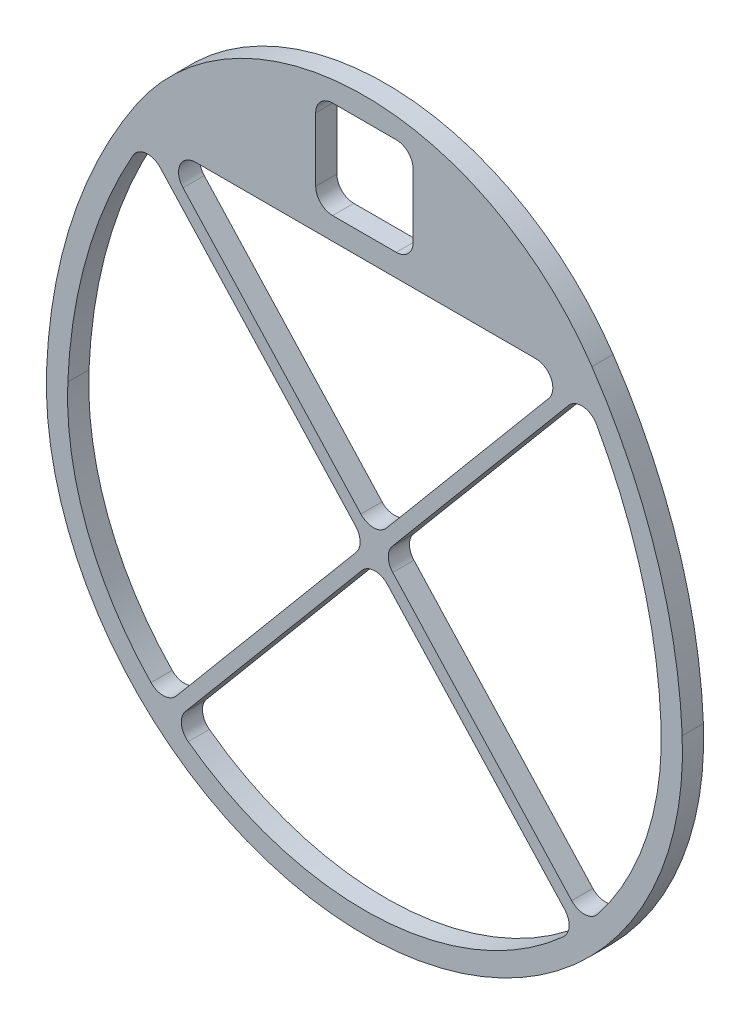
SolidWorks part; units mm, degrees
material "Balsa"
ref_plane "Front Plane" through (0, 0, 0) normal (0, 0, 1) x (1, 0, 0)
ref_plane "Top Plane" through (0, 0, 0) normal (0, 1, 0) x (1, 0, 0)
ref_plane "Right Plane" through (0, 0, 0) normal (1, 0, 0) x (0, 0, -1)
sketch "Sketch1" plane through (0, 0, 0) normal (0, 0, 1) x (1, 0, 0)
  line L8 (-88.9, 0) -> (88.9, 0) construction
  line L9 (-68.1884, 82.55) -> (68.1884, 82.55)
  line L10 (-64.77, 76.2) -> (64.77, 76.2)
  line L21 (-95.2446, 0.2624) -> (-88.9, 0)
  line L22 (88.9, 0) -> (95.2446, 0.2624)
  arc A0 (64.77, 76.2) -> (88.9, 0) centre (-63.3698, -6.2982) cw
  arc A1 (-64.77, 76.2) -> (-88.9, 0) centre (63.3698, -6.2982) ccw
  arc A2 (-68.1884, 82.55) -> (-95.2446, 0.2624) centre (63.3698, -6.2982) ccw
  arc A3 (68.1884, 82.55) -> (95.2446, 0.2624) centre (-63.3698, -6.2982) cw
  arc A4 (-70.1092, 79.6374) -> (-95.2446, 0.2624) centre (63.3698, -6.2982) ccw construction
  arc A5 (70.1092, 79.6374) -> (95.2446, 0.2624) centre (-63.3698, -6.2982) cw construction
  arc A6 (64.77, 76.2) -> (88.9, 0) centre (-63.3698, -6.2982) cw construction
  arc A7 (-64.77, 76.2) -> (-88.9, 0) centre (63.3698, -6.2982) ccw construction
  arc A8 (-68.1884, 82.55) -> (68.1884, 82.55) centre (0, 36.4988) cw
  arc A9 (-88.9, 0) -> (88.9, 0) centre (0, -3.6771) ccw
  arc A10 (-95.2446, 0.2624) -> (95.2446, 0.2624) centre (0, -3.6771) ccw
  point P0 (0, 0)
  point P13 (0, 76.2)
  dimension "D7" = 177.8
  dimension "D2" = 152.4
  dimension "D3" = 76.2
  dimension "D6" = 129.54
  dimension "D1" = 6.35
  dimension "D4" = 6.35
  dimension "D5" = 6.35
extrude "Boss-Extrude1" add sketch "Sketch1" along normal blind 6.35
sketch "Sketch2" plane through (0, 0, 6.35) normal (0, 0, 1) x (1, 0, 0)
  line L0 (0, 76.2) -> (0, 118.7811) construction
  line L1 (-14.605, 112.0955) -> (14.605, 112.0955)
  line L2 (-14.605, 112.0955) -> (-14.605, 82.8855)
  line L3 (-14.605, 82.8855) -> (14.605, 82.8855)
  line L4 (14.605, 112.0955) -> (14.605, 82.8855)
  line L5 (-14.605, 112.0955) -> (14.605, 82.8855) construction
  line L6 (-14.605, 82.8855) -> (14.605, 112.0955) construction
  line L7 (-64.77, 76.2) -> (64.77, 76.2) construction
  arc A0 (68.1884, 82.55) -> (-68.1884, 82.55) centre (0, 36.4988) ccw construction
  point P0 (0, 97.4905)
  point P15 (0, 97.4905)
  dimension "D1" = 29.21
  dimension "D2" = 29.21
extrude "Cut-Extrude1" cut sketch "Sketch2" against normal up to next
fillet "Fillet1" radius 5.08 4 edges at (14.605, 82.8855, 3.175) (14.605, 112.0955, 3.175) (-14.605, 112.0955, 3.175) (-14.605, 82.8855, 3.175)
sketch "Sketch3" plane through (0, 0, 6.35) normal (0, 0, 1) x (1, 0, 0)
  line L0 (-66.1729, 74.9112) -> (66.1428, -69.117)
  line L1 (-66.1729, 74.9112) -> (-63.3671, 77.4888)
  line L2 (66.1428, -69.117) -> (68.9485, -66.5394)
  line L3 (-63.3671, 77.4888) -> (68.9485, -66.5394)
  line L4 (63.3107, 77.4245) -> (-62.4057, -72.3985)
  line L5 (63.3107, 77.4245) -> (66.2293, 74.9755)
  line L6 (-62.4057, -72.3985) -> (-59.4871, -74.8475)
  line L7 (66.2293, 74.9755) -> (-59.4871, -74.8475)
  line L8 (-64.77, 76.2) -> (64.77, 76.2) construction
  point P0 (-64.77, 76.2)
  point P7 (64.77, 76.2)
  arc M17 (88.9, 0) -> (-88.9, 0) centre (0, -3.6771) cw
  arc M18 (-88.9, 0) -> (-64.77, 76.2) centre (63.3698, -6.2982) cw
  line M19 (-64.77, 76.2) -> (64.77, 76.2)
  arc M20 (64.77, 76.2) -> (88.9, 0) centre (-63.3698, -6.2982) cw
  dimension "D1" = 3.81
  dimension "D2" = 3.81
  dimension "D3" = 47.427
  dimension "D4" = 50
  dimension "D5" = 195.58
  dimension "D6" = 195.58
extrude "Boss-Extrude2" add sketch "Sketch3" against normal up to surface (6.35 mm away) contours L4 L3 L0 M19 M18 | L7 L4 L3 M20 M19 | L3 L7 L0 M17 | L7 L3 L4 L0 | L7 L0 L4 M17 up to face at (0, 97.4905, 0)
fillet "Fillet2" radius 5.08 12 edges at (62.2832, 76.2, 3.175) (-62.1831, 76.2, 3.175) (0.3977, 2.4478, 3.175) (-59.9275, -69.445, 3.175) (-65.827, 74.5347, 3.175) (5.4669, 2.5616, 3.175) (65.8408, 74.5125, 3.175) (66.0087, -63.3393, 3.175) (2.9971, -0.3817, 3.175) (63.3872, -66.1174, 3.175) (-57.0564, -71.9508, 3.175) (2.8675, 5.3911, 3.175)
